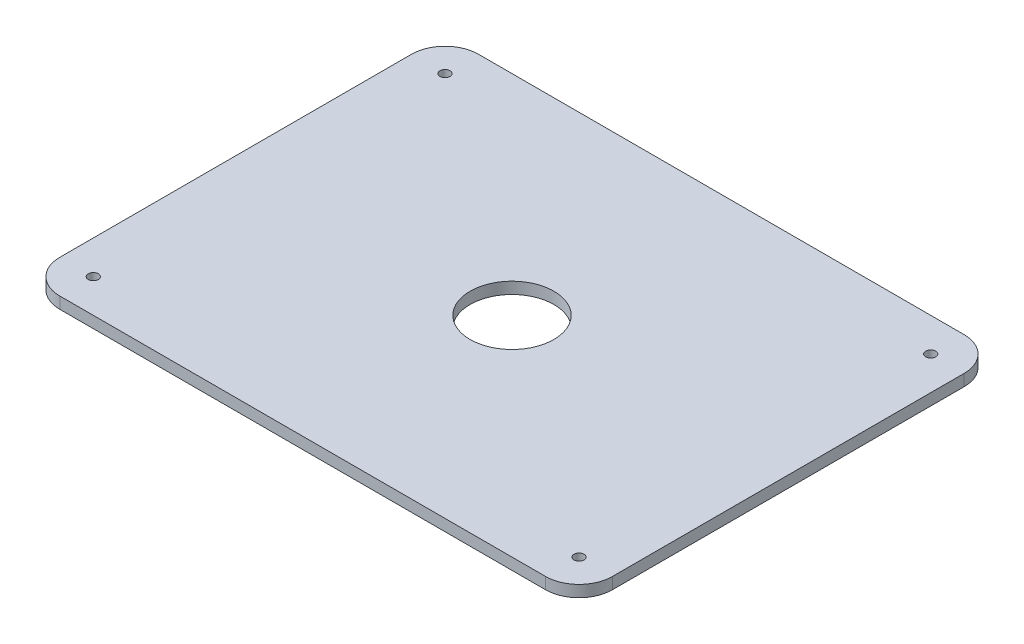
SolidWorks part; units mm, degrees
material "Delrin 2700 NC010, Low Viscosity Acetal Copolymer (SS)"
ref_plane "Front Plane" through (0, 0, 0) normal (0, 0, 1) x (1, 0, 0)
ref_plane "Top Plane" through (0, 0, 0) normal (0, 1, 0) x (1, 0, 0)
ref_plane "Right Plane" through (0, 0, 0) normal (1, 0, 0) x (0, 0, -1)
sketch "Sketch1" plane through (0, 0, 0) normal (0, 1, 0) x (1, 0, 0)
  line L0 (165, 125) -> (-165, -125) construction
  line L5 (-165, -125) -> (165, -125)
  line L6 (-165, -125) -> (-165, 125)
  line L7 (-165, 125) -> (165, 125)
  line L8 (165, -125) -> (165, 125)
  point P5 (0, 0)
  dimension "D1" = 330
  dimension "D2" = 250
extrude "Boss-Extrude1" add sketch "Sketch1" along normal blind 6.9
sketch "Sketch2" plane through (0, 6.9, 0) normal (0, 1, 0) x (1, 0, 0)
  line L0 (145, 105) -> (-145, -105) construction
  line L1 (-145, 105) -> (145, 105) construction
  line L2 (-145, 105) -> (-145, -105) construction
  line L3 (-145, -105) -> (145, -105) construction
  line L4 (145, 105) -> (145, -105) construction
  line L5 (0, 105) -> (0, 125) construction
  line L6 (165, 125) -> (-165, 125) construction
  line L8 (-145, 0) -> (-165, 0) construction
  line L9 (-165, 125) -> (-165, -125) construction
  circle A0 centre (-145, 105) radius 3
  circle A1 centre (145, 105) radius 3
  circle A2 centre (145, -105) radius 3
  circle A3 centre (-145, -105) radius 3
  point P4 (0, 0)
  dimension "D2" = 6
  dimension "D1" = 20
extrude "Cut-Extrude1" cut sketch "Sketch2" against normal through all
sketch "Sketch3" plane through (0, 6.9, 0) normal (0, 1, 0) x (1, 0, 0)
  circle A0 centre (0, 0) radius 25
  point P2 (0, 0)
  dimension "D1" = 50
extrude "Cut-Extrude2" cut sketch "Sketch3" against normal through all
fillet "Fillet1" radius 20 4 edges at (165, 3.45, -125) (-165, 3.45, -125) (-165, 3.45, 125) (165, 3.45, 125)
